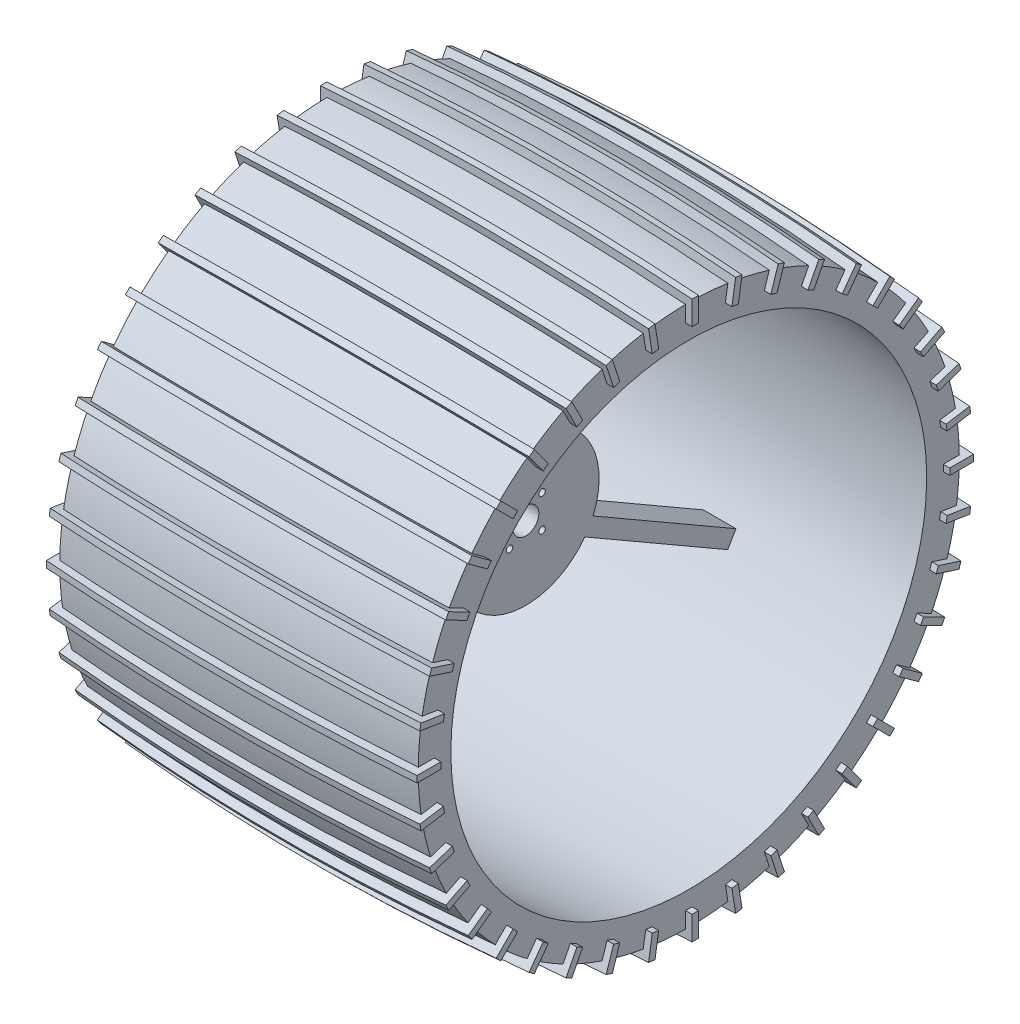
SolidWorks part; units mm, degrees
ref_plane "Alzado" through (0, 0, 0) normal (0, 0, 1) x (1, 0, 0)
ref_plane "Planta" through (0, 0, 0) normal (0, 1, 0) x (1, 0, 0)
ref_plane "Vista lateral" through (0, 0, 0) normal (1, 0, 0) x (0, 0, -1)
sketch "Croquis2" plane through (0, 0, 0) normal (0, 0, 1) x (1, 0, 0)
  line L0 (0, 0) -> (0, 75) construction
  line L1 (0, 75) -> (0, 85) construction
  line L2 (-55, 73) -> (55, 73) construction
  line L3 (-55, 83) -> (55, 83) construction
  line L4 (-55, 73) -> (-55, 83)
  line L5 (55, 73) -> (55, 83)
  arc A0 (55, 73) -> (-55, 73) centre (0, -682.25) ccw
  arc A1 (55, 83) -> (-55, 83) centre (0, -672.25) ccw
  point P7 (0, 73)
  point P10 (0, 83)
  dimension "D1" = 75
  dimension "D2" = 10
  dimension "D3" = 110
  dimension "D4" = 2
  dimension "D5" = 2
sketch "Croquis4" plane through (0, 0, 0) normal (0, 1, 0) x (1, 0, 0)
  line L0 (-55, 0) -> (55, 0) construction
  line L1 (-55, 0) -> (55, 0) construction
  point P6 (0, 0)
revolve "Revolución1" add sketch "Croquis2" angle 360 about L0
sketch "Croquis5" plane through (0, 0, 0) normal (0, 0, 1) x (1, 0, 0)
  line L0 (0, 85) -> (0, 87) construction
  line L1 (-55, 83) -> (55, 83) construction
  line L2 (-1.01, 85) -> (1.01, 85) construction
  line L10 (57, 85.3999) -> (57, 78.0758)
  line L11 (57, 78.0758) -> (-57, 78.0758)
  line L12 (-57, 78.0758) -> (-57, 85.1067)
  arc A0 (55, 83) -> (-55, 83) centre (0, -672.25) ccw construction
  arc A3 (57, 85.3999) -> (-57, 85.1067) centre (1.9425, -669.995) ccw
  point P8 (-0.0055, 87.4012)
  point P15 (0, 85)
  dimension "D1" = 2
  dimension "D2" = 114
  dimension "D3" = 2.4012
extrude "Saliente-Extruir6" add sketch "Croquis5" along normal mid plane 2
pattern_circular "MatrizC1" count 40 over 360 about axis through (0, 0, 0) along (1, 0, 0) of "Saliente-Extruir6"
sketch "Croquis9" plane through (0, 0, 0) normal (1, 0, 0) x (0, 0, -1)
  circle A0 centre (0, 0) radius 4
  circle A1 centre (0, 0) radius 22.5
  dimension "D1" = 45
extrude "Saliente-Extruir7" add sketch "Croquis9" along normal mid plane 10 separate body
sketch "Croquis11" plane through (0, 0, 0) normal (1, 0, 0) x (0, 0, -1)
  line L0 (0, 0) -> (0, 73) construction
  line L1 (2.5, 73) -> (-2.5, 73)
  line L2 (0, 17.7987) -> (-2.5, 17.7987) construction
  line L3 (0, 17.7987) -> (2.5, 17.7987)
  line L4 (2.5, 73) -> (2.5, 17.7987)
  line L5 (-2.5, 73) -> (-2.5, 17.7987)
  line L6 (-2.5, 17.7987) -> (0, 17.7987)
  circle A0 centre (0, 0) radius 73 construction
  point P9 (0, 73)
  dimension "D1" = 5
  dimension "D2" = 5
extrude "Saliente-Extruir8" add sketch "Croquis11" along normal mid plane 10
pattern_circular "MatrizC2" count 3 over 360 about axis through (0, 0, 0) along (1, 0, 0) of "Saliente-Extruir8"
sketch "Croquis13" plane through (5, 0, 0) normal (1, 0, 0) x (0, 0, -1)
  line L5 (-5, -5) -> (5, 5) construction
  line L6 (-5, 5) -> (5, -5) construction
  circle A1 centre (-5, 5) radius 1
  circle A2 centre (5, 5) radius 1
  circle A3 centre (5, -5) radius 1
  circle A4 centre (-5, -5) radius 1
  dimension "D3" = 2
  dimension "D2" = 10
extrude "Cortar-Extruir3" cut sketch "Croquis13" against normal blind 15
